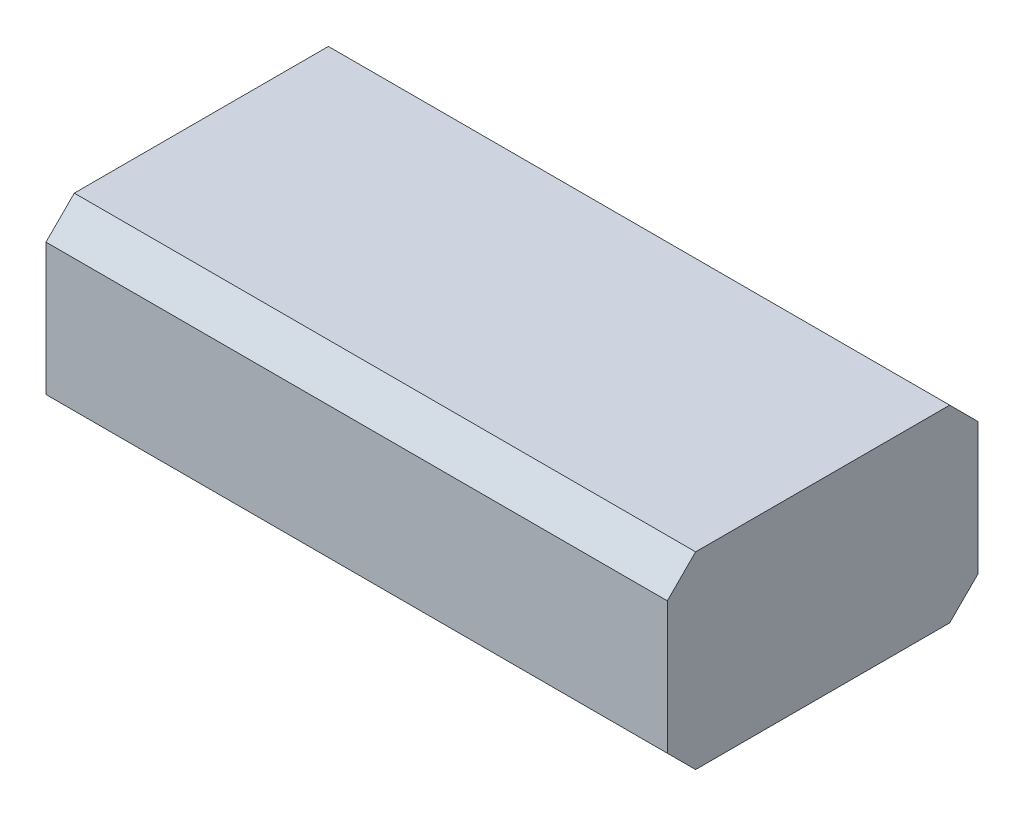
SolidWorks part; units mm, degrees
ref_plane "Top Plane" through (0, 0, 0) normal (0, 0, 1) x (1, 0, 0)
ref_plane "Front Plane" through (0, 0, 0) normal (0, 1, 0) x (1, 0, 0)
ref_plane "Right Plane" through (0, 0, 0) normal (1, 0, 0) x (0, 0, -1)
sketch "Sketch1" plane through (0, 0, 0) normal (0, 0, 1) x (1, 0, 0)
  line L1 (0, 0) -> (0.659, 0)
  line L2 (0, 0) -> (0, 0.2)
  line L3 (0, 0.2) -> (0.659, 0.2)
  line L4 (0.659, 0) -> (0.659, 0.2)
  dimension "D1" = 0.659
  dimension "D2" = 0.2
extrude "Boss-Extrude1" add sketch "Sketch1" along normal blind 0.3295
chamfer "Chamfer1" distance 0.03 angle 45 4 edges at (0.3295, 0.2, 0) (0.3295, 0, 0) (0.3295, 0.2, 0.3295) (0.3295, 0, 0.3295)
